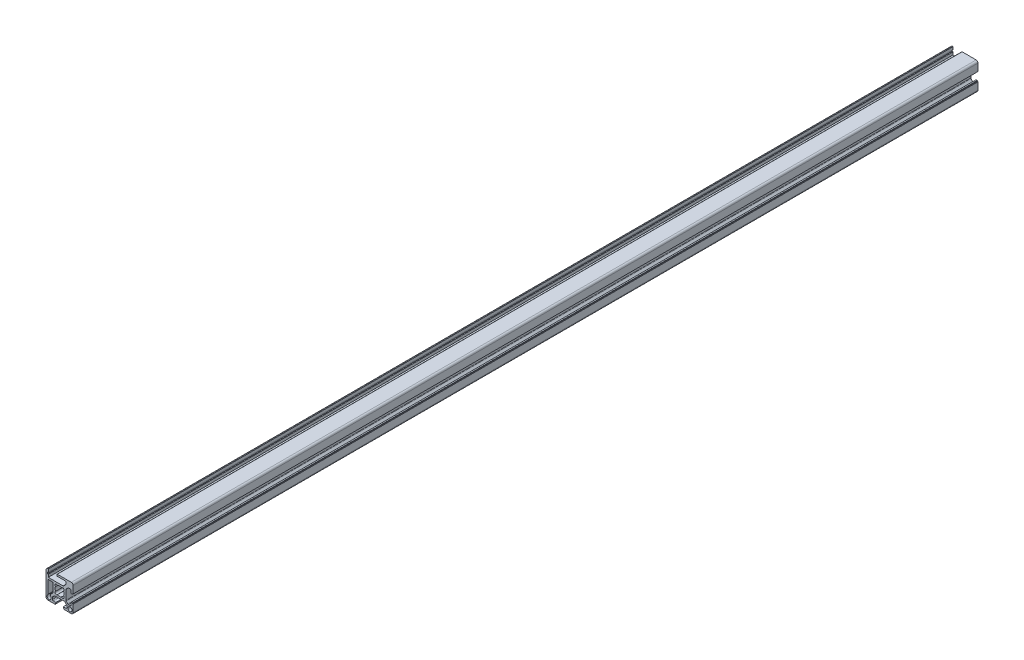
SolidWorks part; units mm, degrees
ref_plane "前视基准面" through (0, 0, 0) normal (0, 0, 1) x (1, 0, 0)
ref_plane "上视基准面" through (0, 0, 0) normal (0, 1, 0) x (1, 0, 0)
ref_plane "右视基准面" through (0, 0, 0) normal (1, 0, 0) x (0, 0, -1)
sketch "草图1" plane through (0, 0, 0) normal (0, 0, 1) x (1, 0, 0)
  line L0 (97.9982, 104.1812) -> (97.9982, 105.1903)
  line L1 (98.2911, 105.8974) -> (100.7053, 108.3117)
  line L2 (100.9982, 109.0188) -> (100.9982, 117.6045)
  line L3 (99.9982, 118.6045) -> (95.1982, 118.6045)
  line L4 (95.1982, 118.6045) -> (95.1982, 104.4007)
  line L5 (94.4982, 123.6038) -> (95.4982, 123.6038)
  line L6 (95.4982, 123.6038) -> (95.4982, 120.6045)
  line L7 (95.4982, 120.6045) -> (111.7556, 120.6045)
  line L8 (112.4627, 120.8974) -> (114.7053, 123.1401)
  line L9 (114.9982, 123.8472) -> (114.9982, 125.6045)
  line L10 (113.9982, 126.6045) -> (104.9982, 126.6045)
  line L11 (104.9982, 126.6045) -> (104.9982, 128.1045)
  line L12 (105.4982, 128.6045) -> (120.9982, 128.6045)
  line L13 (122.9982, 126.6045) -> (122.9982, 118.5045)
  line L14 (122.9982, 118.5045) -> (122.1982, 118.5045)
  line L15 (122.1982, 118.5045) -> (122.1982, 117.7045)
  line L16 (122.1982, 117.7045) -> (120.7982, 117.7045)
  line L17 (120.7982, 117.7045) -> (120.7982, 120.6045)
  line L18 (119.7982, 121.6045) -> (117.8266, 121.6045)
  line L19 (117.1195, 121.3117) -> (115.2911, 119.4832)
  line L20 (114.9982, 118.7761) -> (114.9982, 108.433)
  line L21 (115.2911, 107.7259) -> (117.1195, 105.8974)
  line L22 (117.8266, 105.6045) -> (119.7982, 105.6045)
  line L23 (120.7982, 106.6045) -> (120.7982, 109.5045)
  line L24 (120.7982, 109.5045) -> (122.1982, 109.5045)
  line L25 (122.1982, 109.5045) -> (122.1982, 108.7045)
  line L26 (122.1982, 108.7045) -> (122.9982, 108.7045)
  line L27 (122.9982, 108.7045) -> (122.9982, 100.6045)
  line L28 (120.9982, 98.6045) -> (112.8982, 98.6045)
  line L29 (112.8982, 98.6045) -> (112.8982, 99.4045)
  line L30 (112.8982, 99.4045) -> (112.0982, 99.4045)
  line L31 (112.0982, 99.4045) -> (112.0982, 100.8045)
  line L32 (112.0982, 100.8045) -> (114.9982, 100.8045)
  line L33 (115.9982, 101.8045) -> (115.9982, 103.7761)
  line L34 (115.7053, 104.4832) -> (113.8769, 106.3117)
  line L35 (113.1698, 106.6045) -> (102.8266, 106.6045)
  line L36 (102.1195, 106.3117) -> (100.2911, 104.4832)
  line L37 (99.9982, 103.7761) -> (99.9982, 101.8045)
  line L38 (100.9982, 100.8045) -> (103.8982, 100.8045)
  line L39 (103.8982, 100.8045) -> (103.8982, 99.4045)
  line L40 (103.8982, 99.4045) -> (103.0982, 99.4045)
  line L41 (103.0982, 99.4045) -> (103.0982, 98.6045)
  line L42 (103.0982, 98.6045) -> (94.9982, 98.6045)
  line L43 (92.9982, 100.6045) -> (92.9982, 126.6045)
  line L44 (94.9982, 128.6045) -> (95.4982, 128.6045)
  line L45 (95.4982, 128.6045) -> (95.4982, 125.6038)
  line L46 (95.4982, 125.6038) -> (94.4982, 125.6038)
  line L47 (94.4982, 125.6038) -> (94.4982, 123.6038)
  circle A0 centre (119.4982, 102.1045) radius 2.25
  arc A1 (103.5731, 115.9323) -> (103.5731, 111.2768) centre (107.9982, 113.6045) ccw
  arc A2 (103.5731, 111.2768) -> (105.6704, 109.1795) centre (104.4627, 110.069) ccw
  arc A3 (105.6704, 109.1795) -> (110.326, 109.1795) centre (107.9982, 113.6045) ccw
  arc A4 (110.326, 109.1795) -> (112.4233, 111.2768) centre (111.5338, 110.069) ccw
  arc A5 (112.4233, 111.2768) -> (112.4233, 115.9323) centre (107.9982, 113.6045) ccw
  arc A6 (112.4233, 115.9323) -> (110.326, 118.0296) centre (111.5338, 117.1401) ccw
  arc A7 (110.326, 118.0296) -> (105.6704, 118.0296) centre (107.9982, 113.6045) ccw
  arc A8 (105.6704, 118.0296) -> (103.5731, 115.9323) centre (104.4627, 117.1401) ccw
  arc A9 (97.9982, 104.1812) -> (98.229, 103.5422) centre (98.9982, 104.1812) ccw
  arc A10 (98.2911, 105.8974) -> (97.9982, 105.1903) centre (98.9982, 105.1903) ccw
  arc A11 (100.7053, 108.3117) -> (100.9982, 109.0188) centre (99.9982, 109.0188) ccw
  arc A12 (100.9982, 117.6045) -> (99.9982, 118.6045) centre (99.9982, 117.6045) ccw
  arc A13 (94.9059, 103.6942) -> (95.1982, 104.4007) centre (94.1982, 104.4007) ccw
  arc A14 (94.9059, 103.6942) -> (98.229, 103.5422) centre (96.4982, 102.1045) ccw
  arc A15 (111.7556, 120.6045) -> (112.4627, 120.8974) centre (111.7556, 121.6045) ccw
  arc A16 (114.7053, 123.1401) -> (114.9982, 123.8472) centre (113.9982, 123.8472) ccw
  arc A17 (114.9982, 125.6045) -> (113.9982, 126.6045) centre (113.9982, 125.6045) ccw
  arc A18 (105.4982, 128.6045) -> (104.9982, 128.1045) centre (105.4982, 128.1045) ccw
  arc A19 (122.9982, 126.6045) -> (120.9982, 128.6045) centre (120.9982, 126.6045) ccw
  arc A20 (120.7982, 120.6045) -> (119.7982, 121.6045) centre (119.7982, 120.6045) ccw
  arc A21 (117.8266, 121.6045) -> (117.1195, 121.3117) centre (117.8266, 120.6045) ccw
  arc A22 (115.2911, 119.4832) -> (114.9982, 118.7761) centre (115.9982, 118.7761) ccw
  arc A23 (114.9982, 108.433) -> (115.2911, 107.7259) centre (115.9982, 108.433) ccw
  arc A24 (117.1195, 105.8974) -> (117.8266, 105.6045) centre (117.8266, 106.6045) ccw
  arc A25 (119.7982, 105.6045) -> (120.7982, 106.6045) centre (119.7982, 106.6045) ccw
  arc A26 (120.9982, 98.6045) -> (122.9982, 100.6045) centre (120.9982, 100.6045) ccw
  arc A27 (114.9982, 100.8045) -> (115.9982, 101.8045) centre (114.9982, 101.8045) ccw
  arc A28 (115.9982, 103.7761) -> (115.7053, 104.4832) centre (114.9982, 103.7761) ccw
  arc A29 (113.8769, 106.3117) -> (113.1698, 106.6045) centre (113.1698, 105.6045) ccw
  arc A30 (102.8266, 106.6045) -> (102.1195, 106.3117) centre (102.8266, 105.6045) ccw
  arc A31 (100.2911, 104.4832) -> (99.9982, 103.7761) centre (100.9982, 103.7761) ccw
  arc A32 (99.9982, 101.8045) -> (100.9982, 100.8045) centre (100.9982, 101.8045) ccw
  arc A33 (92.9982, 100.6045) -> (94.9982, 98.6045) centre (94.9982, 100.6045) ccw
  arc A34 (94.9982, 128.6045) -> (92.9982, 126.6045) centre (94.9982, 126.6045) ccw
extrude "拉伸1" add sketch "草图1" along normal blind 1000
